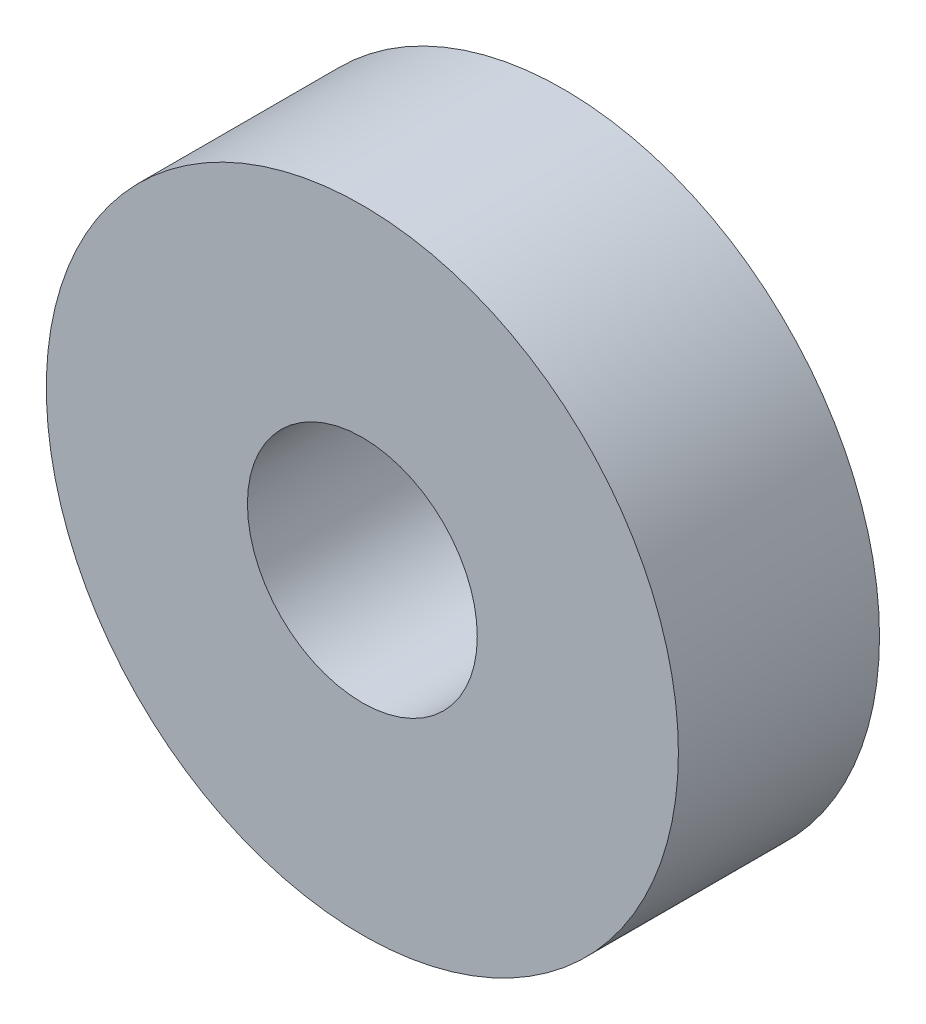
SolidWorks part; units mm, degrees
ref_plane "Alzado" through (0, 0, 0) normal (0, 0, 1) x (1, 0, 0)
ref_plane "Planta" through (0, 0, 0) normal (0, 1, 0) x (1, 0, 0)
ref_plane "Vista lateral" through (0, 0, 0) normal (1, 0, 0) x (0, 0, -1)
sketch "Croquis1" plane through (0, 0, 0) normal (0, 0, 1) x (1, 0, 0)
  circle A0 centre (0, 0) radius 11
  circle A1 centre (0, 0) radius 4
  dimension "D1" = 8
  dimension "D2" = 22
extrude "Saliente-Extruir1" add sketch "Croquis1" along normal blind 7
